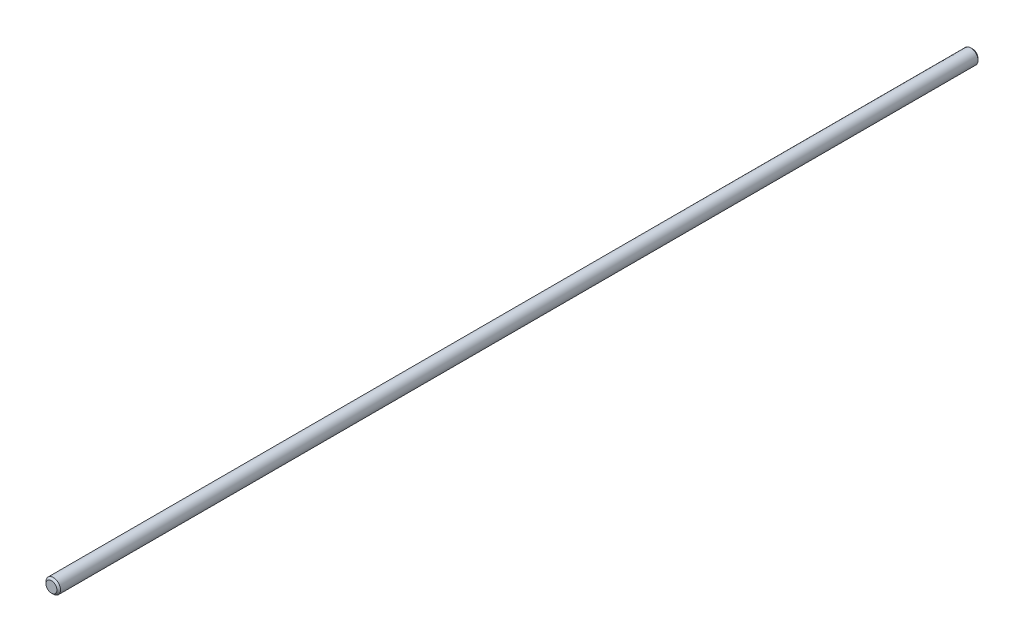
SolidWorks part; units mm, degrees
ref_plane "Front Plane" through (0, 0, 0) normal (0, 0, 1) x (1, 0, 0)
ref_plane "Top Plane" through (0, 0, 0) normal (0, 1, 0) x (1, 0, 0)
ref_plane "Right Plane" through (0, 0, 0) normal (1, 0, 0) x (0, 0, -1)
sketch "Sketch1" plane through (0, 0, 0) normal (0, 0, 1) x (1, 0, 0)
  circle A0 centre (0, 0) radius 4
  dimension "D1" = 8
extrude "Boss-Extrude1" add sketch "Sketch1" along normal blind 507
chamfer "Chamfer1" distance 1 angle 45 2 edges at (4, 0, 507) (4, 0, 0)
